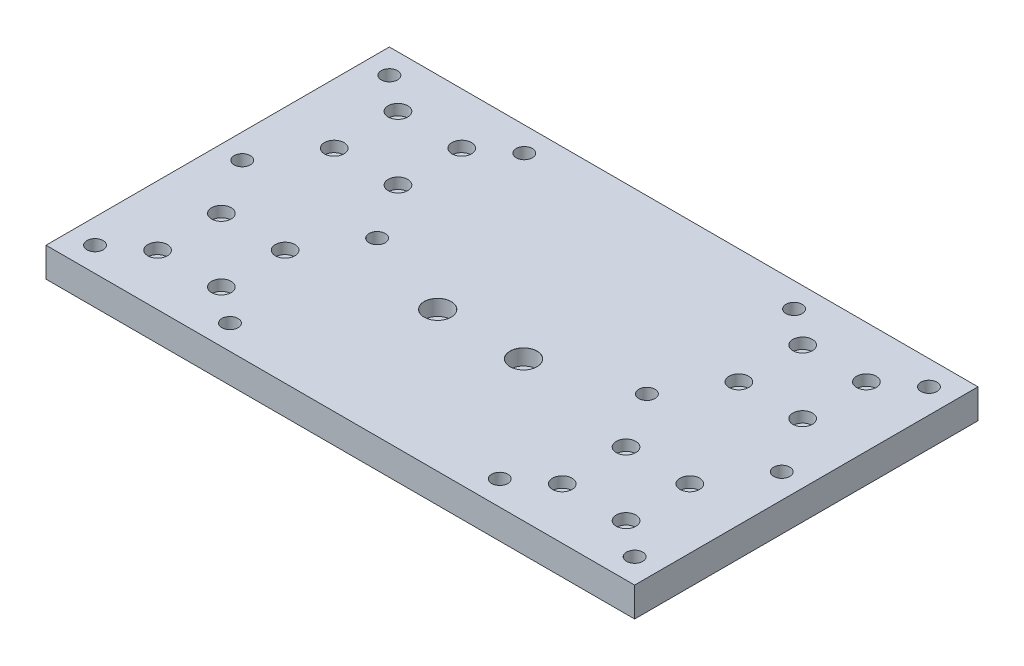
SolidWorks part; units mm, degrees
material "1023 Листовая углеродистая сталь (SS)"
ref_plane "Front" through (0, 0, 0) normal (0, 0, 1) x (1, 0, 0)
ref_plane "Top" through (0, 0, 0) normal (0, 1, 0) x (1, 0, 0)
ref_plane "Right" through (0, 0, 0) normal (1, 0, 0) x (0, 0, -1)
sketch "Sketch1" plane through (0, 0, 0) normal (0, 1, 0) x (1, 0, 0)
  line L0 (0, -47) -> (0, 47) construction
  line L1 (-95.5, 49) -> (-69.5, 49) construction
  line L2 (-95.5, 49) -> (-95.5, 23) construction
  line L3 (-95.5, 23) -> (-69.5, 23) construction
  line L4 (-69.5, 49) -> (-69.5, 23) construction
  line L5 (0, 0) -> (-59.385, 0) construction
  line L6 (69.5, 49) -> (69.5, 23) construction
  line L7 (95.5, 23) -> (69.5, 23) construction
  line L8 (95.5, 49) -> (95.5, 23) construction
  line L9 (95.5, 49) -> (69.5, 49) construction
  line L10 (95.5, -49) -> (69.5, -49) construction
  line L11 (95.5, -49) -> (95.5, -23) construction
  line L12 (95.5, -23) -> (69.5, -23) construction
  line L13 (69.5, -49) -> (69.5, -23) construction
  line L14 (-69.5, -49) -> (-69.5, -23) construction
  line L15 (-95.5, -23) -> (-69.5, -23) construction
  line L16 (-95.5, -49) -> (-95.5, -23) construction
  line L17 (-95.5, -49) -> (-69.5, -49) construction
  dimension "D1" = 26
  dimension "D2" = 26
  dimension "D3" = 69.5
  dimension "D4" = 23
sketch "Sketch2" plane through (0, 0, 0) normal (0, 1, 0) x (1, 0, 0)
  line L0 (0, -47) -> (0, 47) construction
  line L1 (-120, 70) -> (120, 70)
  line L2 (-120, 70) -> (-120, -70)
  line L3 (-120, -70) -> (120, -70)
  line L4 (120, 70) -> (120, -70)
  line L5 (-120, 70) -> (120, -70) construction
  line L6 (-120, -70) -> (120, 70) construction
  point P0 (0, 0)
  dimension "D1" = 140
  dimension "D2" = 240
extrude "Extrude1" add sketch "Sketch2" along normal blind 12
hole_wizard "CBORE for M4 Hex Socket Head Cap Screw1" positions "Sketch5" profile "Sketch6" counterbore size "M4" standard "DIN" end condition through all
sketch "Sketch5" plane through (0, 12, 0) normal (0, 1, 0) x (1, 0, 0)
  point P0 (-95.5, 49)
  point P3 (-69.5, 49)
  point P6 (-69.5, 23)
  point P9 (-95.5, 23)
  point P12 (-95.5, -23)
  point P15 (-69.5, -23)
  point P18 (-69.5, -49)
  point P21 (-95.5, -49)
  point P24 (69.5, 49)
  point P27 (95.5, 49)
  point P30 (95.5, 23)
  point P33 (69.5, 23)
  point P36 (69.5, -23)
  point P39 (95.5, -23)
  point P42 (95.5, -49)
  point P45 (69.5, -49)
sketch "Sketch6" plane through (-95.5, 12, -49) normal (1, 0, 0) x (0, 0, 1)
  line L0 (0, 0) -> (0, 12)
  line L1 (0, 12) -> (2.25, 12)
  line L3 (2.25, 12) -> (2.25, 4.4)
  line L4 (2.25, 4.4) -> (4, 4.4)
  line L5 (4, 4.4) -> (4, 0)
  line L7 (4, 0) -> (0, 0)
  line L11 (0, -6.35) -> (0, 107.95) construction
  dimension "Диаметр сквозного отверстия" = 4.5
  dimension "Глубина сквозного отверстия" = 12
  dimension "Диаметр цековки" = 8
  dimension "Глубина цековки" = 4.4
hole_wizard "CBORE for M6 Hex Socket Head Cap Screw1" positions "Sketch7" profile "Sketch8" counterbore size "M6" standard "DIN" end condition through all
sketch "Sketch7" plane through (0, 0, 0) normal (0, -1, 0) x (-1, 0, 0)
  line L0 (120, 70) -> (120, -70) construction
  line L1 (120, -70) -> (-120, -70) construction
  line L2 (-120, 70) -> (120, 70) construction
  line L3 (95.5, -49) -> (69.5, -49)
  line L5 (82.5, -49) -> (82.5, -29.8612) construction
  line L7 (0, 0) -> (0, -34.8181) construction
  line L9 (-82.5, -49) -> (-82.5, -29.8612) construction
  line L10 (-95.5, -49) -> (-69.5, -49)
  point P0 (110, -60)
  point P2 (110, 0)
  point P4 (110, 60)
  point P26 (55, 60)
  point P27 (55, 0)
  point P28 (55, -60)
  point P36 (-55, -60)
  point P37 (-55, 0)
  point P38 (-55, 60)
  point P39 (-110, 60)
  point P40 (-110, 0)
  point P41 (-110, -60)
  dimension "D1" = 10
  dimension "D2" = 10
  dimension "D3" = 10
sketch "Sketch8" plane through (-110, 0, 60) normal (1, 0, 0) x (0, 0, -1)
  line L0 (0, 0) -> (0, 12)
  line L1 (0, 12) -> (3.3, 12)
  line L3 (3.3, 12) -> (3.3, 6.4)
  line L4 (3.3, 6.4) -> (5.5, 6.4)
  line L5 (5.5, 6.4) -> (5.5, 0)
  line L7 (5.5, 0) -> (0, 0)
  line L11 (0, -6.35) -> (0, 107.95) construction
  dimension "Диаметр сквозного отверстия" = 6.6
  dimension "Глубина сквозного отверстия" = 12
  dimension "Диаметр цековки" = 11
  dimension "Глубина цековки" = 6.4
hole_wizard "CBORE for M6 Hex Socket Head Cap Screw2" positions "Sketch9" profile "Sketch10" counterbore size "M6" standard "DIN"
sketch "Sketch9" plane through (0, 12, 0) normal (0, 1, 0) x (1, 0, 0)
  point P0 (17.5, -12.8)
  point P3 (-17.5, -12.8)
sketch "Sketch10" plane through (17.5, 12, 12.8) normal (1, 0, 0) x (0, 0, 1)
  line L0 (0, 0) -> (0, 13.4828)
  line L1 (0, 13.4828) -> (3.3, 11.5)
  line L2 (3.3, 11.5) -> (3.3, 6.4)
  line L3 (3.3, 6.4) -> (5.5, 6.4)
  line L5 (5.5, 6.4) -> (5.5, 0.025)
  line L6 (5.5, 0.025) -> (5.525, 0)
  line L7 (5.525, 0) -> (0, 0)
  line L8 (-5.5, 0.025) -> (-5.525, 0) construction
  line L10 (0, 13.4828) -> (-3.3, 11.5) construction
  line L11 (0, -6.35) -> (0, 107.95) construction
  dimension "Диаметр отверстия" = 6.6
  dimension "Глубина отверстия" = 11.5
  dimension "Диаметр цековки" = 11
  dimension "Глубина цековки" = 6.4
  dimension "Диаметр передней зенковки" = 11.05
  dimension "Угол передней зенковки" = 90
  dimension "Угол заточки сверла" = 118
